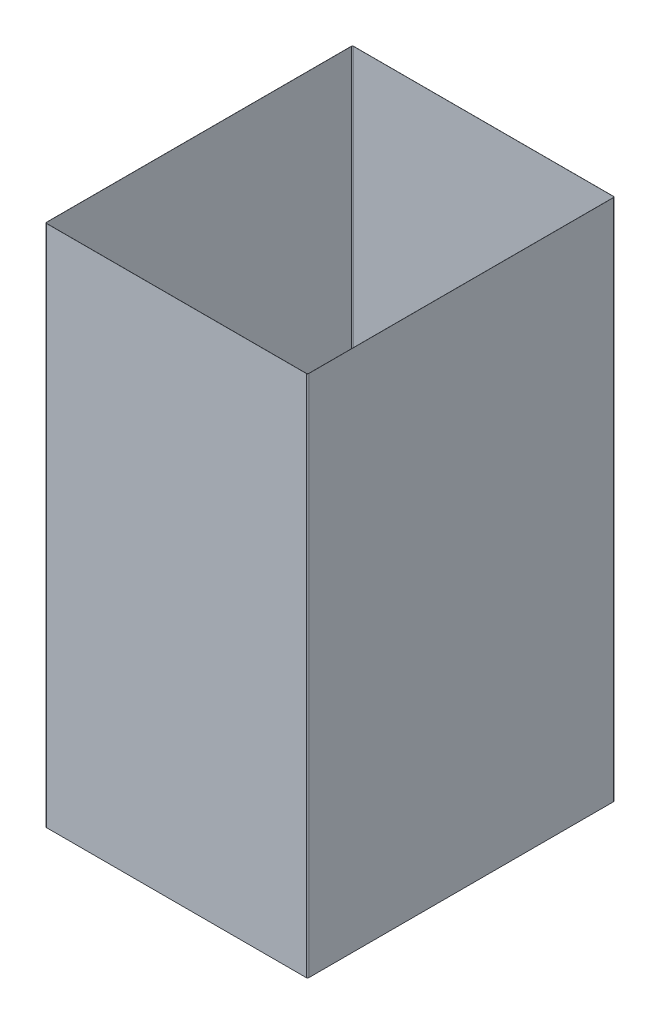
SolidWorks part; units mm, degrees
ref_plane "Front" through (0, 0, 0) normal (0, 0, 1) x (1, 0, 0)
ref_plane "Top" through (0, 0, 0) normal (0, 1, 0) x (1, 0, 0)
ref_plane "Right" through (0, 0, 0) normal (1, 0, 0) x (0, 0, -1)
sketch "Sketch1" plane through (0, 0, 0) normal (0, 1, 0) x (1, 0, 0)
  line L1 (1, 0) -> (241.7, 0)
  line L2 (0, 1) -> (0, 283.25)
  line L3 (1, 284.25) -> (241.7, 284.25)
  line L4 (242.7, 1) -> (242.7, 283.25)
  arc A0 (241.7, 284.25) -> (242.7, 283.25) centre (241.7, 283.25) cw
  arc A1 (241.7, 0) -> (242.7, 1) centre (241.7, 1) ccw
  arc A2 (1, 0) -> (0, 1) centre (1, 1) cw
  arc A3 (0, 283.25) -> (1, 284.25) centre (1, 283.25) cw
  point P9 (242.7, 0)
  point P12 (0, 0)
  point P15 (0, 284.25)
  dimension "D3" = 1
  dimension "D1" = 284.25
  dimension "D2" = 242.7
extrude "Extrude-Thin1" add sketch "Sketch1" along normal blind 484.8 thin
